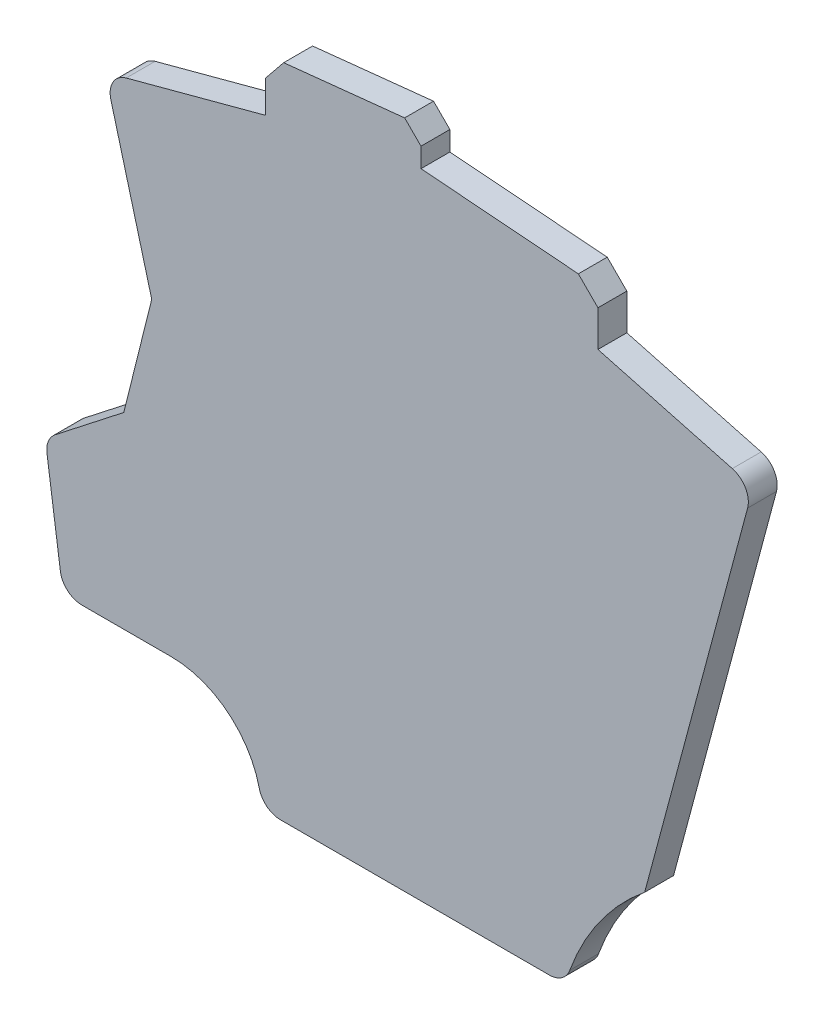
SolidWorks part; units mm, degrees
ref_plane "Front Plane" through (0, 0, 0) normal (0, 0, 1) x (1, 0, 0)
ref_plane "Top Plane" through (0, 0, 0) normal (0, 1, 0) x (1, 0, 0)
ref_plane "Right Plane" through (0, 0, 0) normal (1, 0, 0) x (0, 0, -1)
sketch "Sketch1" plane through (0, 0, 0) normal (0, 0, 1) x (1, 0, 0)
  line L0 (-49.4165, -244.8125) -> (743.9169, -244.8125) construction
  line L1 (38.961, 13.16) -> (42.961, 13.16)
  line L2 (38.961, 13.16) -> (38.961, -13.16)
  line L3 (38.961, -13.16) -> (42.961, -13.16)
  line L4 (42.961, 13.16) -> (42.961, -13.16)
  line L6 (-22.8189, -33.5966) -> (43.1811, -33.5966)
  line L7 (-22.8189, -33.5966) -> (-22.8189, -46.6075)
  line L8 (-22.8189, -46.6075) -> (43.1811, -46.6075)
  line L9 (43.1811, -33.5966) -> (43.1811, -46.6075)
  line L19 (-146.7546, -45.6733) -> (-104.7346, -45.6733)
  line L24 (-159.2446, -33.6733) -> (-174.2446, -33.6733)
  line L25 (-176.7041, -16.1733) -> (-174.2446, -33.6733)
  line L26 (-176.7041, -16.1733) -> (-165.8246, -7.6733)
  line L27 (-165.8246, -7.6733) -> (-161.96, 7.8267)
  line L28 (-161.96, 7.8267) -> (-168.3908, 31.8267)
  line L29 (-168.3908, 31.8267) -> (-146.1745, 37.7796)
  line L30 (-146.1745, 37.7796) -> (-146.1745, 45.0796)
  line L31 (-146.1745, 45.0796) -> (-124.6745, 47.3355)
  line L32 (-124.6745, 47.3355) -> (-124.6745, 42.1355)
  line L33 (-124.6745, 42.1355) -> (-100.1745, 40.2073)
  line L34 (-100.1745, 40.2073) -> (-100.1745, 32.7073)
  line L35 (-100.1745, 32.7073) -> (-78.6745, 26.9464)
  line L36 (-78.6745, 26.9464) -> (-93.7054, -29.1497)
  circle A4 centre (-159.2446, -46.1733) radius 12.5
  circle A9 centre (-72.6099, -55.1733) radius 33.5
  point P11 (-125.7446, -45.6733)
  point P31 (0, 0)
  dimension "D10" = 17.5
  dimension "D15" = 24
  dimension "D20" = 21.5
  dimension "D27" = 21.5
  dimension "D2" = 0.5
  dimension "D3" = 25
  dimension "D4" = 67
  dimension "D1" = 4
  dimension "D5" = 9.5
  dimension "D6" = 33.5
  dimension "D7" = 53.1348
  dimension "D8" = 98
  dimension "D9" = 15
  dimension "D11" = 8.5
  dimension "D12" = 120
  dimension "D13" = 142
  dimension "D14" = 15.5
  dimension "D16" = 151
  dimension "D17" = 23
  dimension "D18" = 105
  dimension "D19" = 7.3
  dimension "D21" = 5.2
  dimension "D22" = 24.5
  dimension "D23" = 94.5
  dimension "D24" = 7.5
  dimension "D25" = 94.5
  dimension "D26" = 105
extrude "Boss-Extrude2" add sketch "Sketch1" along normal blind 4 contours A9 L36 L35 L34 L33 L32 L31 L30 L29 L28 L27 L26 L25 L24 A4 L19
fillet "Fillet3" radius 3 6 edges at (-78.6745, 26.9464, 2) (-168.3908, 31.8267, 2) (-176.7041, -16.1733, 2) (-104.7346, -45.6733, 2) (-174.2446, -33.6733, 2) (-146.7546, -45.6733, 2)
chamfer "Chamfer1" distance 2.5 angle 45 3 edges at (-146.1745, 45.0796, 2) (-124.6745, 47.3355, 2) (-100.1745, 40.2073, 2)
